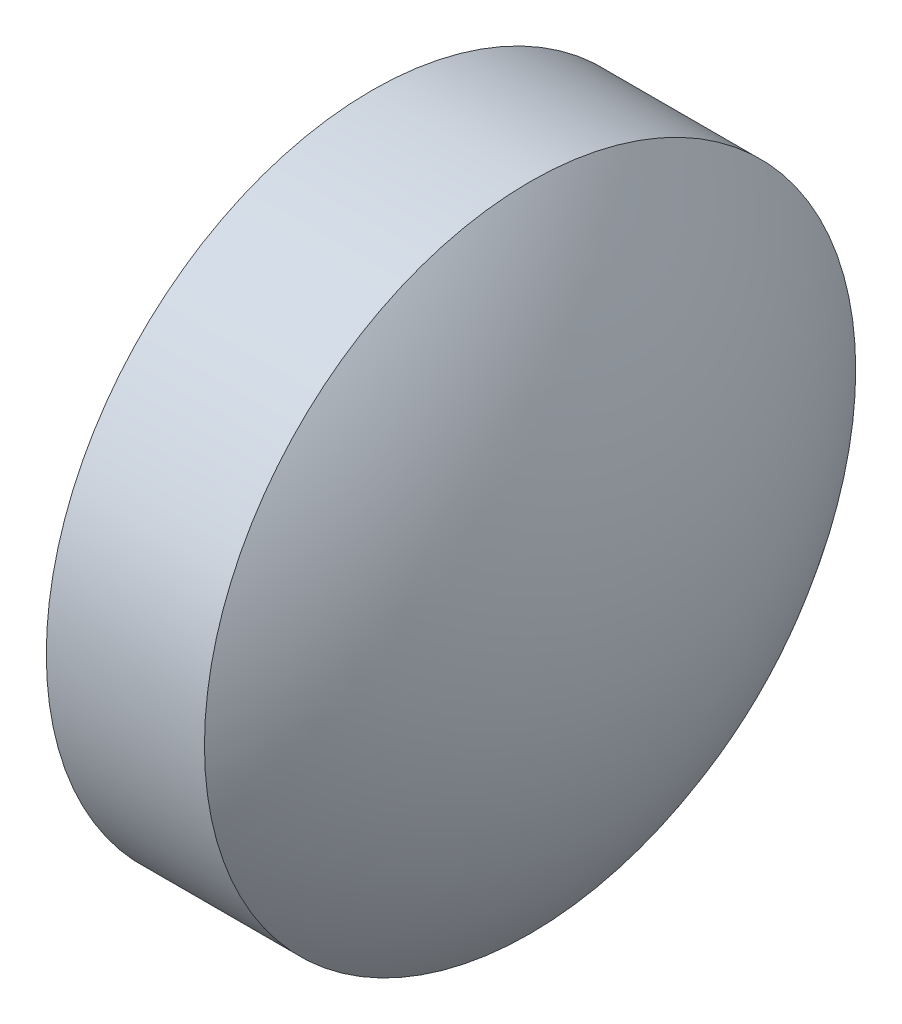
SolidWorks part; units mm, degrees
ref_plane "前视基准面" through (0, 0, 0) normal (0, 0, 1) x (1, 0, 0)
ref_plane "上视基准面" through (0, 0, 0) normal (0, 1, 0) x (1, 0, 0)
ref_plane "右视基准面" through (0, 0, 0) normal (1, 0, 0) x (0, 0, -1)
sketch "草图2" plane through (0, 0, 0) normal (0, 0, 1) x (1, 0, 0)
  line L0 (486.4778, 143.6688) -> (491.8561, 143.6688) construction
  line L1 (486.9675, 143.6688) -> (486.9675, 146.8188)
  line L2 (486.9675, 146.8188) -> (488.4975, 146.8188)
  line L3 (486.9675, 143.6688) -> (489.5675, 143.6688)
  arc A0 (489.5675, 143.6688) -> (488.4975, 146.8188) centre (484.3958, 143.6688) ccw
revolve "旋转2" add sketch "草图2" angle 360 about L0
